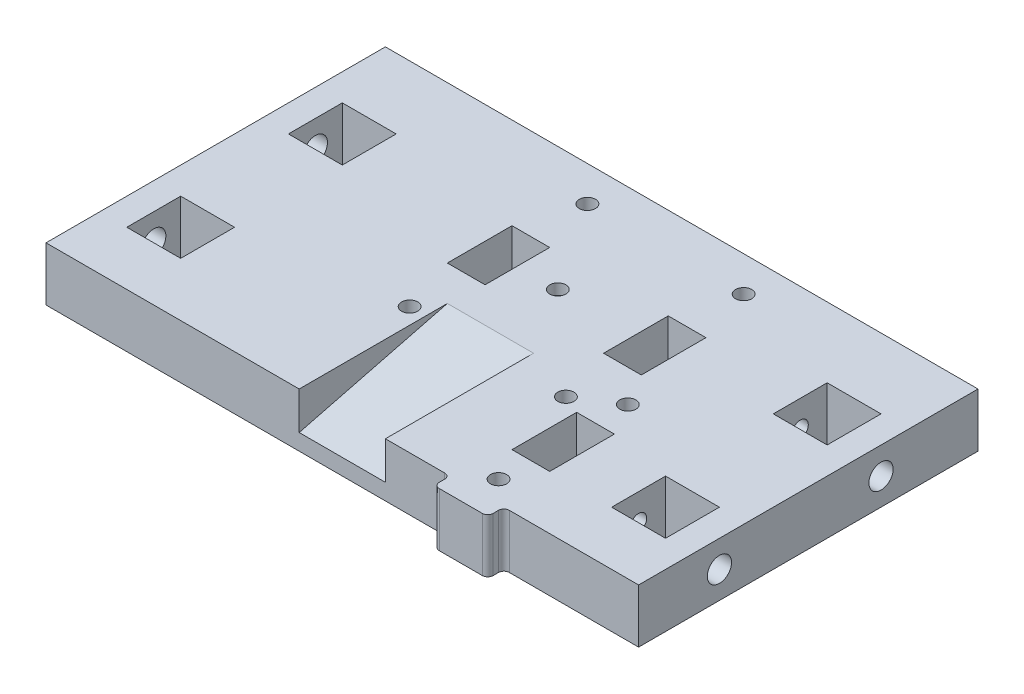
SolidWorks part; units mm, degrees
ref_plane "Alzado" through (0, 0, 0) normal (0, 0, 1) x (1, 0, 0)
ref_plane "Planta" through (0, 0, 0) normal (0, 1, 0) x (1, 0, 0)
ref_plane "Vista lateral" through (0, 0, 0) normal (1, 0, 0) x (0, 0, -1)
sketch "Croquis1" plane through (0, 0, 0) normal (0, 1, 0) x (1, 0, 0)
  line L0 (-50, 0) -> (55, 0) construction
  line L1 (0, 7.5) -> (-6.4952, 3.75)
  line L2 (-6.4952, 3.75) -> (-6.4952, -3.75)
  line L3 (-6.4952, -3.75) -> (0, -7.5)
  line L4 (0, -7.5) -> (6.4952, -3.75)
  line L5 (6.4952, -3.75) -> (6.4952, 3.75)
  line L6 (6.4952, 3.75) -> (0, 7.5)
  line L7 (-50, 20) -> (50, 20) construction
  line L8 (-50, -40) -> (50, -40) construction
  line L9 (-50, 10) -> (50, 10) construction
  line L10 (-50, 20) -> (-40, 20)
  line L11 (-50, 20) -> (-50, -40)
  line L12 (-50, -40) -> (-40, -40)
  line L13 (-40, 20) -> (-40, -40)
  line L14 (50, 20) -> (40, 20)
  line L15 (50, 20) -> (50, -40)
  line L16 (50, -40) -> (40, -40)
  line L17 (40, 20) -> (40, -40)
  line L18 (-40, 20) -> (40, 20)
  line L19 (-40, 20) -> (-40, -40)
  line L20 (-40, -40) -> (40, -40)
  line L21 (40, 20) -> (40, -40)
  line L22 (-50, -20) -> (50, -20) construction
  line L23 (-50, -30) -> (50, -30) construction
  line L24 (-14.5, 12.5) -> (21.5, 12.5) construction
  line L25 (-50, 10) -> (-40, 10)
  line L26 (-50, 10) -> (-50, 0)
  line L27 (-50, 0) -> (-40, 0)
  line L28 (-40, 10) -> (-40, 0)
  line L29 (50, 10) -> (40, 10)
  line L30 (50, 10) -> (50, 0)
  line L31 (50, 0) -> (40, 0)
  line L32 (40, 10) -> (40, 0)
  line L33 (50, -20) -> (40, -20)
  line L34 (50, -20) -> (50, -30)
  line L35 (50, -30) -> (40, -30)
  line L36 (40, -20) -> (40, -30)
  line L37 (-50, -20) -> (-40, -20)
  line L38 (-50, -20) -> (-50, -30)
  line L39 (-50, -30) -> (-40, -30)
  line L40 (-40, -20) -> (-40, -30)
  line L41 (-50, 20) -> (-55, 20)
  line L42 (-50, 20) -> (-50, -40)
  line L43 (-50, -40) -> (-55, -40)
  line L44 (-55, 20) -> (-55, -40)
  line L45 (50, 20) -> (55, 20)
  line L46 (50, 20) -> (50, -40)
  line L47 (50, -40) -> (55, -40)
  line L48 (55, 20) -> (55, -40)
  line L49 (-14.5, -12.5) -> (21.5, -12.5) construction
  line L50 (-11, 12.5) -> (-11, -12.5) construction
  line L51 (-14.5, 12.5) -> (-7.5, 12.5)
  line L52 (-14.5, 12.5) -> (-14.5, -12.5)
  line L53 (-14.5, -12.5) -> (-7.5, -12.5)
  line L54 (-7.5, 12.5) -> (-7.5, -12.5)
  line L55 (21.5, 12.5) -> (14.5, 12.5)
  line L56 (21.5, 12.5) -> (21.5, -12.5)
  line L57 (21.5, -12.5) -> (14.5, -12.5)
  line L58 (14.5, 12.5) -> (14.5, -12.5)
  line L59 (-14.5, 6) -> (-7.5, 6)
  line L60 (-14.5, 6) -> (-14.5, -6)
  line L61 (-14.5, -6) -> (-7.5, -6)
  line L62 (-7.5, 6) -> (-7.5, -6)
  line L63 (14.5, 6) -> (21.5, 6)
  line L64 (14.5, 6) -> (14.5, -6)
  line L65 (14.5, -6) -> (21.5, -6)
  line L66 (21.5, 6) -> (21.5, -6)
  line L67 (18, 12.5) -> (18, -12.5) construction
  circle A0 centre (0, 0) radius 7.5 construction
  circle A1 centre (-11, 16.5) radius 1.5
  circle A2 centre (18, 16.5) radius 1.5
  circle A3 centre (-11, -16.5) radius 1.5
  circle A4 centre (18, -16.5) radius 1.5
  dimension "D1" = 15
  dimension "D24" = 3
  dimension "D25" = 3
  dimension "D26" = 3
  dimension "D27" = 3
  dimension "D2" = 100
  dimension "D3" = 10
  dimension "D4" = 10
  dimension "D5" = 20
  dimension "D6" = 50
  dimension "D7" = 60
  dimension "D8" = 10
  dimension "D9" = 20
  dimension "D10" = 10
  dimension "D11" = 5
  dimension "D12" = 5
  dimension "D13" = 40
  dimension "D14" = 7
  dimension "D15" = 7
  dimension "D16" = 25
  dimension "D17" = 12.5
  dimension "D18" = 7.5
  dimension "D19" = 14.5
  dimension "D20" = 12
  dimension "D21" = 12
  dimension "D22" = 6.5
  dimension "D23" = 6.5
  dimension "D28" = 4
  dimension "D29" = 4
  dimension "D30" = 4
  dimension "D31" = 4
  dimension "D32" = 3.5
  dimension "D33" = 3.5
  dimension "D34" = 3.5
  dimension "D35" = 3.5
extrude "Saliente-Extruir1" add sketch "Croquis1" along normal blind 10 contours L13 L19 L20 L17 L21 L18 A4 A3 A2 A1 L58 L55 L56 L57 L6 L5 L4 L3 L2 L1 L51 L54 L53 L52 | L11 L37 L13 L27 | L39 L11 L12 L13 | L41 L44 L43 L11 | L11 L25 L13 L10 | L29 L15 L14 L17 | L48 L45 L15 L47 | L33 L15 L31 L17 | L15 L35 L17 L16 | L52 L59 L54 L51 | L61 L52 L53 L54 | L58 L63 L56 L55 | L65 L58 L57 L56
sketch "Croquis2" plane through (0, 0, 0) normal (0, -1, 0) x (1, 0, 0)
  line L1 (-6.9585, 16.5) -> (-8.9793, 20)
  line L2 (-8.9793, 20) -> (-13.0207, 20)
  line L3 (-13.0207, 20) -> (-15.0415, 16.5)
  line L4 (-15.0415, 16.5) -> (-13.0207, 13)
  line L5 (-13.0207, 13) -> (-8.9793, 13)
  line L6 (-8.9793, 13) -> (-6.9585, 16.5)
  line L7 (22.0415, 16.5) -> (20.0207, 20)
  line L8 (20.0207, 20) -> (15.9793, 20)
  line L9 (15.9793, 20) -> (13.9585, 16.5)
  line L10 (13.9585, 16.5) -> (15.9793, 13)
  line L11 (15.9793, 13) -> (20.0207, 13)
  line L12 (20.0207, 13) -> (22.0415, 16.5)
  line L13 (-6.9585, -16.5) -> (-8.9793, -13)
  line L14 (-8.9793, -13) -> (-13.0207, -13)
  line L15 (-13.0207, -13) -> (-15.0415, -16.5)
  line L16 (-15.0415, -16.5) -> (-13.0207, -20)
  line L17 (-13.0207, -20) -> (-8.9793, -20)
  line L18 (-8.9793, -20) -> (-6.9585, -16.5)
  line L19 (22.0415, -16.5) -> (20.0207, -13)
  line L20 (20.0207, -13) -> (15.9793, -13)
  line L21 (15.9793, -13) -> (13.9585, -16.5)
  line L22 (13.9585, -16.5) -> (15.9793, -20)
  line L23 (15.9793, -20) -> (20.0207, -20)
  line L24 (20.0207, -20) -> (22.0415, -16.5)
  circle A0 centre (-11, 16.5) radius 3.5 construction
  circle A1 centre (18, 16.5) radius 3.5 construction
  circle A2 centre (-11, -16.5) radius 3.5 construction
  circle A3 centre (18, -16.5) radius 3.5 construction
  dimension "D1" = 7
  dimension "D2" = 7
  dimension "D3" = 7
  dimension "D4" = 7
extrude "Cortar-Extruir1" cut sketch "Croquis2" against normal blind 5
sketch "Croquis3" plane through (55, 0, 0) normal (1, 0, 0) x (0, 0, -1)
  line L0 (-40, 5) -> (20, 5) construction
  line L1 (-40, 10) -> (-40, 0) construction
  line L2 (20, 10) -> (20, 0) construction
  circle A0 centre (-25, 5) radius 1.5
  circle A1 centre (5, 5) radius 1.5
  dimension "D3" = 3
  dimension "D4" = 3
  dimension "D1" = 15
  dimension "D2" = 15
extrude "Cortar-Extruir2" cut sketch "Croquis3" against normal blind 25
sketch "Croquis6" plane through (-55, 0, 0) normal (-1, 0, 0) x (0, 0, 1)
  line L0 (-20, 5) -> (40, 5) construction
  line L1 (-20, 10) -> (-20, 0) construction
  line L2 (40, 10) -> (40, 0) construction
  circle A0 centre (-5, 5) radius 1.5
  circle A1 centre (25, 5) radius 1.5
  dimension "D1" = 3
  dimension "D2" = 3
  dimension "D3" = 15
  dimension "D4" = 15
extrude "Cortar-Extruir3" cut sketch "Croquis6" against normal blind 25
sketch "Croquis8" plane through (0, 10, 0) normal (0, 1, 0) x (1, 0, 0)
  line L0 (-7.5, 6) -> (-7.5, -6) construction
  line L1 (7.5, -8.9193) -> (-7.5, -8.9193)
  line L2 (7.5, -8.9193) -> (7.5, 8.9193)
  line L3 (7.5, 8.9193) -> (-7.5, 8.9193)
  line L4 (-7.5, -8.9193) -> (-7.5, 8.9193)
  line L5 (7.5, -8.9193) -> (-7.5, 8.9193) construction
  line L6 (7.5, 8.9193) -> (-7.5, -8.9193) construction
  circle A0 centre (0, 0) radius 1.5
  point P0 (0, 0)
  dimension "D1" = 3
extrude "Saliente-Extruir2" add sketch "Croquis8" against normal blind 2
sketch "Croquis9" plane through (55, 0, 0) normal (1, 0, 0) x (0, 0, -1)
  line L0 (-12.5, 10) -> (-40, 3)
  line L1 (-40, 10) -> (0, 10)
  line L2 (-40, 10) -> (-40, 0)
  line L3 (-40, 0) -> (0, 0)
  line L4 (0, 10) -> (0, 0)
  circle M5 centre (-25, 5) radius 1.5
  line M7 (-40, 0) -> (20, 0)
  line M9 (20, 10) -> (-40, 10)
  line M10 (-40, 10) -> (-40, 0)
  dimension "D1" = 12.5
  dimension "D2" = 3
extrude "Cortar-Extruir4" cut sketch "Croquis9" against normal mid plane 16 from offset 55 contours L4 L0 M9 M10 M7 M5 offset against normal yes
sketch "Croquis10" plane through (0, 10, 0) normal (0, 1, 0) x (1, 0, 0)
  line L0 (25, 20) -> (25, -40) construction
  line L1 (-55, 20) -> (55, 20) construction
  line L2 (8, -40) -> (55, -40) construction
  line L4 (21.5, -30) -> (28.5, -30)
  line L5 (21.5, -30) -> (21.5, -18)
  line L6 (21.5, -18) -> (28.5, -18)
  line L7 (28.5, -30) -> (28.5, -18)
  line L8 (21.5, -30) -> (28.5, -18) construction
  line L9 (21.5, -18) -> (28.5, -30) construction
  circle A0 centre (25, -12) radius 1.5
  circle A1 centre (25, -36) radius 1.5
  point P6 (25, -24)
  dimension "D5" = 3
  dimension "D6" = 3
  dimension "D1" = 25
  dimension "D2" = 7
  dimension "D3" = 12
  dimension "D4" = 24
  dimension "D7" = 6
  dimension "D8" = 6
extrude "Cortar-Extruir5" cut sketch "Croquis10" against normal blind 16
sketch "Croquis12" plane through (0, 0, -20) normal (0, 0, -1) x (-1, 0, 0)
  line L1 (-55, 10) -> (55, 10)
  line L2 (-55, 10) -> (-55, 0)
  line L3 (-55, 0) -> (55, 0)
  line L4 (55, 10) -> (55, 0)
extrude "Saliente-Extruir3" add sketch "Croquis12" along normal blind 3
sketch "Croquis13" plane through (0, 0, 0) normal (0, -1, 0) x (1, 0, 0)
  line L1 (29.0415, 12) -> (27.0207, 15.5)
  line L2 (27.0207, 15.5) -> (22.9793, 15.5)
  line L3 (22.9793, 15.5) -> (20.9585, 12)
  line L4 (20.9585, 12) -> (22.9793, 8.5)
  line L5 (22.9793, 8.5) -> (27.0207, 8.5)
  line L6 (27.0207, 8.5) -> (29.0415, 12)
  line L7 (29.0415, 36) -> (27.0207, 39.5)
  line L8 (27.0207, 39.5) -> (22.9793, 39.5)
  line L9 (22.9793, 39.5) -> (20.9585, 36)
  line L10 (20.9585, 36) -> (22.9793, 32.5)
  line L11 (22.9793, 32.5) -> (27.0207, 32.5)
  line L12 (27.0207, 32.5) -> (29.0415, 36)
  circle A0 centre (25, 12) radius 3.5 construction
  circle A1 centre (25, 36) radius 3.5 construction
  dimension "D1" = 7
  dimension "D2" = 7
extrude "Cortar-Extruir6" cut sketch "Croquis13" against normal blind 5
sketch "Croquis14" plane through (0, 0, 0) normal (0, -1, 0) x (1, 0, 0)
  line L0 (-55, 40) -> (55, 40) construction
  line L2 (30, 41) -> (30, 42)
  line L3 (29, 43) -> (21, 43)
  line L4 (20, 41) -> (20, 42)
  line L5 (19, 40) -> (31, 40)
  circle A0 centre (25, 36) radius 1.5 construction
  arc A1 (30, 42) -> (29, 43) centre (29, 42) ccw
  arc A2 (21, 43) -> (20, 42) centre (21, 42) ccw
  arc A3 (20, 41) -> (19, 40) centre (19, 41) cw
  arc A4 (31, 40) -> (30, 41) centre (31, 41) cw
  dimension "D4" = 1
  dimension "D5" = 1
  dimension "D1" = 3
  dimension "D2" = 5
  dimension "D3" = 5
extrude "Saliente-Extruir4" add sketch "Croquis14" against normal blind 10
sketch "Croquis15" plane through (55, 0, 0) normal (1, 0, 0) x (0, 0, -1)
  circle A0 centre (-25, 5) radius 2.25
  circle A1 centre (5, 5) radius 2.25
  dimension "D1" = 4.5
  dimension "D2" = 4.5
extrude "Cortar-Extruir7" cut sketch "Croquis15" against normal blind 10
sketch "Croquis16" plane through (-55, 0, 0) normal (-1, 0, 0) x (0, 0, 1)
  circle A0 centre (-5, 5) radius 2.25
  circle A1 centre (25, 5) radius 2.25
  dimension "D1" = 4.5
  dimension "D2" = 4.5
extrude "Cortar-Extruir8" cut sketch "Croquis16" against normal blind 10
